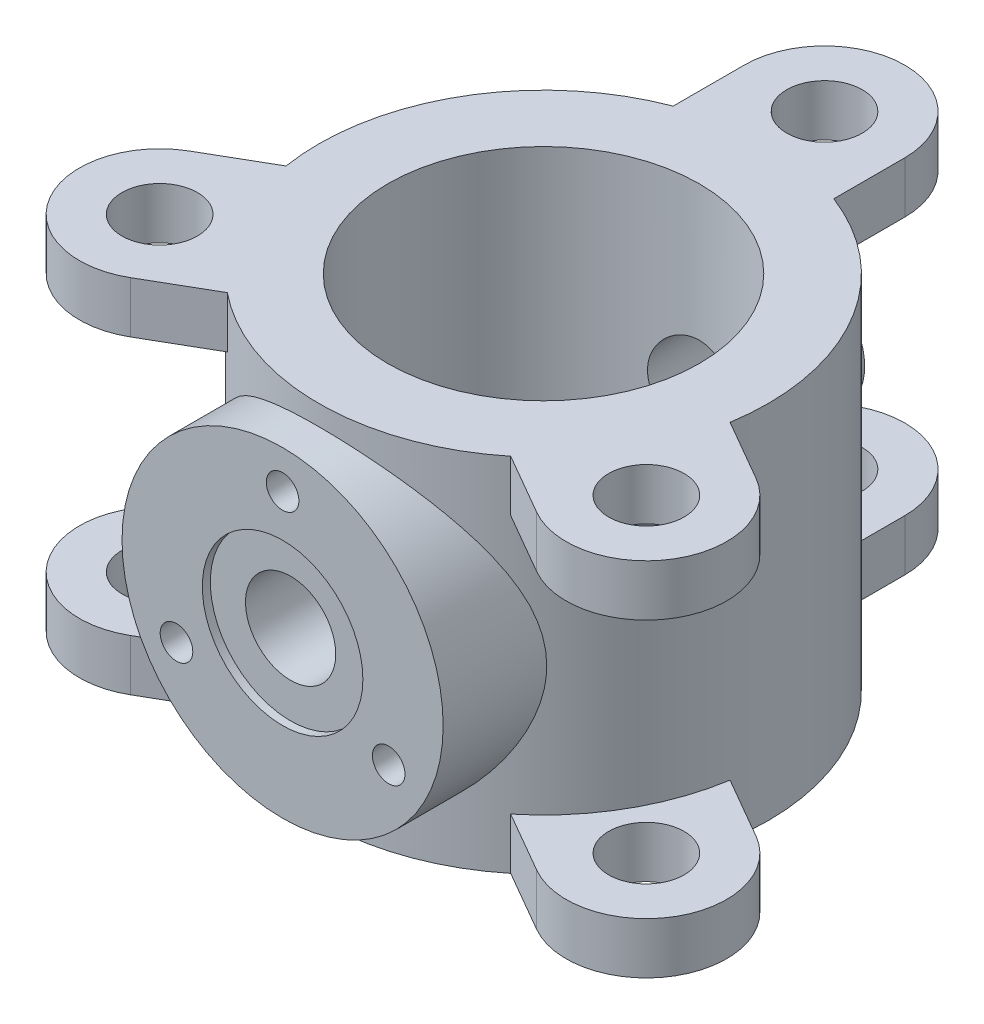
SolidWorks part; units mm, degrees
ref_plane "Front Plane" through (0, 0, 0) normal (0, 0, 1) x (1, 0, 0)
ref_plane "Top Plane" through (0, 0, 0) normal (0, 1, 0) x (1, 0, 0)
ref_plane "Right Plane" through (0, 0, 0) normal (1, 0, 0) x (0, 0, -1)
sketch "Sketch1" plane through (0, 0, 0) normal (0, 1, 0) x (1, 0, 0)
  circle A0 centre (0, 0) radius 140
  circle A1 centre (0, 0) radius 97
  dimension "D1" = 280
  dimension "D2" = 194
extrude "Boss-Extrude1" add sketch "Sketch1" along normal mid plane 225
ref_plane "Plane1" through (0, 0, 162.5) normal (0, 0, 1) x (1, 0, 0)
sketch "Sketch2" plane through (0, 0, 162.5) normal (0, 0, 1) x (1, 0, 0)
  circle A0 centre (0, 0) radius 100
  dimension "D1" = 200
extrude "Boss-Extrude2" add sketch "Sketch2" against normal up to next
ref_plane "Plane2" through (0, 0, -162.5) normal (0, 0, 1) x (1, 0, 0)
sketch "Sketch3" plane through (0, 0, -162.5) normal (0, 0, 1) x (1, 0, 0)
  circle A0 centre (0, 0) radius 37.5
  dimension "D1" = 75
extrude "Boss-Extrude3" add sketch "Sketch3" along normal up to next
hole_wizard "Hole1" positions "Sketch4" profile "Sketch5" legacy
sketch "Sketch4" plane through (0, 0, 162.5) normal (0, 0, 1) x (1, 0, 0)
  point P0 (0, 76.3)
  point P8 (0.9413, 11.1391)
  dimension "D1" = 76.3
sketch "Sketch5" plane through (0, 76.3, 162.5) normal (1, 0, 0) x (0, -1, 0)
  line L0 (0, 0) -> (0, 30)
  line L1 (0, 30) -> (10.15, 30)
  line L2 (10.15, 30) -> (10.15, 0)
  line L3 (10.15, 0) -> (0, 0)
  line L4 (0, 110) -> (0, -10) construction
  dimension "Diameter" = 20.3
  dimension "Depth" = 30
pattern_circular "CirPattern2" count 3 over 360 about axis through (0, 0, 0) along (0, 0, 1) of "Hole1"
hole_wizard "Hole2" positions "Sketch6" profile "Sketch7" legacy
sketch "Sketch6" plane through (0, 0, 162.5) normal (0, 0, 1) x (1, 0, 0)
  point P0 (0, 0)
sketch "Sketch7" plane through (0, 0, 162.5) normal (1, 0, 0) x (0, -1, 0)
  line L0 (0, 0) -> (0, 310)
  line L1 (0, 310) -> (28.1, 310)
  line L2 (28.1, 310) -> (28.1, 5)
  line L3 (28.1, 5) -> (50, 5)
  line L4 (50, 5) -> (50, 0)
  line L5 (50, 0) -> (0, 0)
  line L6 (0, 110) -> (0, -10) construction
  dimension "Diameter" = 56.2
  dimension "Depth" = 310
  dimension "C-Bore Diameter" = 100
  dimension "C-Bore Depth" = 5
sketch "Sketch10" plane through (0, 112.5, 0) normal (0, 1, 0) x (1, 0, 0)
  line L0 (50, 175) -> (50, 130.767)
  line L2 (-50, 130.767) -> (-50, 175)
  arc A0 (50, 175) -> (-50, 175) centre (0, 175) ccw
  circle A1 centre (0, 0) radius 140 construction
  circle A2 centre (0, 0) radius 140
  circle M2 centre (0, 0) radius 140
  dimension "D2" = 100
  dimension "D1" = 175
extrude "Boss-Extrude6" add sketch "Sketch10" against normal blind 32 contours L0 A0 L2 M2
pattern_circular "CirPattern5" count 3 over 360 about axis through (0, 0, 0) along (0, 1, 0) of "Boss-Extrude6"
hole_wizard "Hole3" positions "Sketch15" profile "Sketch16" legacy
sketch "Sketch15" plane through (0, 112.5, 0) normal (0, 1, 0) x (1, 0, 0)
  point P0 (0, 175)
  point P3 (151.5544, -87.5)
  point P6 (-151.5544, -87.5)
sketch "Sketch16" plane through (0, 112.5, -175) normal (1, 0, 0) x (0, 0, 1)
  line L0 (0, 0) -> (0, 32)
  line L1 (0, 32) -> (23.5, 32)
  line L2 (23.5, 32) -> (23.5, 0)
  line L3 (23.5, 0) -> (0, 0)
  line L4 (0, 110) -> (0, -10) construction
  dimension "Diameter" = 47
  dimension "Depth" = 32
mirror "Mirror1" about plane through (0, 0, 0) normal (0, 1, 0) of "Hole3", "CirPattern5", "Boss-Extrude6"
